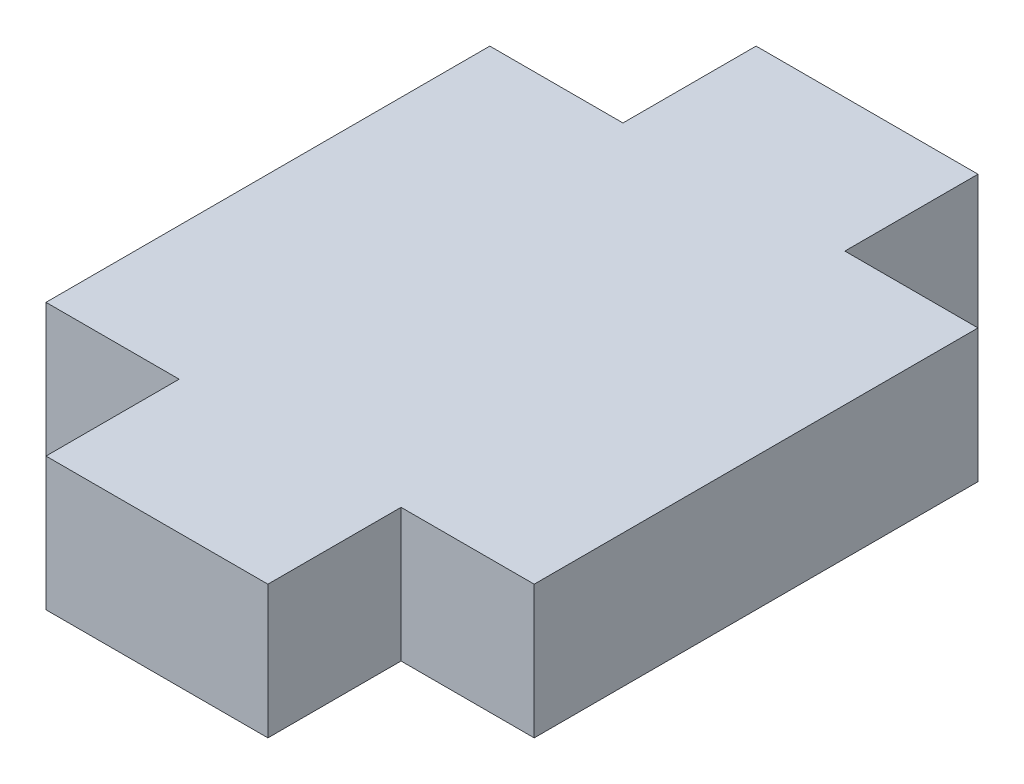
SolidWorks part; units mm, degrees
ref_plane "Front Plane" through (0, 0, 0) normal (0, 0, 1) x (1, 0, 0)
ref_plane "Top Plane" through (0, 0, 0) normal (0, 1, 0) x (1, 0, 0)
ref_plane "Right Plane" through (0, 0, 0) normal (1, 0, 0) x (0, 0, -1)
sketch "Sketch1" plane through (0, 0, 0) normal (0, 1, 0) x (1, 0, 0)
  line L0 (-5.5, 5) -> (-5.5, -5)
  line L1 (-5.5, -5) -> (-2.5, -5)
  line L2 (-2.5, -5) -> (-2.5, -8)
  line L3 (-2.5, -8) -> (2.5, -8)
  line L4 (2.5, -8) -> (2.5, -5)
  line L5 (2.5, -5) -> (5.5, -5)
  line L6 (5.5, -5) -> (5.5, 5)
  line L7 (5.5, 5) -> (2.5, 5)
  line L8 (2.5, 5) -> (2.5, 8)
  line L9 (2.5, 8) -> (-2.5, 8)
  line L10 (-2.5, 8) -> (-2.5, 5)
  line L11 (-2.5, 5) -> (-5.5, 5)
  point P2 (0, 8)
  point P13 (5.5, 0)
  dimension "D1" = 3
  dimension "D2" = 10
  dimension "D3" = 5
extrude "Boss-Extrude1" add sketch "Sketch1" along normal mid plane 3
